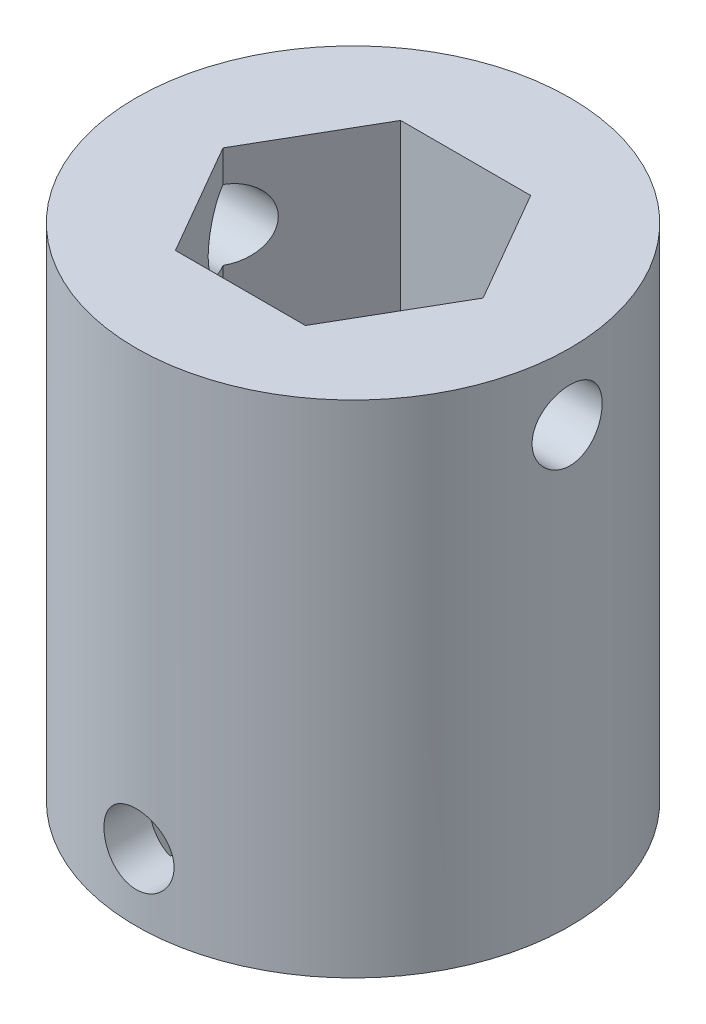
SolidWorks part; units mm, degrees
ref_plane "Front Plane" through (0, 0, 0) normal (0, 0, 1) x (1, 0, 0)
ref_plane "Top Plane" through (0, 0, 0) normal (0, 1, 0) x (1, 0, 0)
ref_plane "Right Plane" through (0, 0, 0) normal (1, 0, 0) x (0, 0, -1)
sketch "Sketch1" plane through (0, 0, 0) normal (0, 1, 0) x (1, 0, 0)
  line L1 (7.7942, 0) -> (3.8971, 6.75)
  line L2 (3.8971, 6.75) -> (-3.8971, 6.75)
  line L3 (-3.8971, 6.75) -> (-7.7942, 0)
  line L4 (-7.7942, 0) -> (-3.8971, -6.75)
  line L5 (-3.8971, -6.75) -> (3.8971, -6.75)
  line L6 (3.8971, -6.75) -> (7.7942, 0)
  circle A0 centre (0, 0) radius 13
  circle A1 centre (0, 0) radius 6.75 construction
  dimension "D2" = 26
  dimension "D1" = 13.5
extrude "Boss-Extrude1" add sketch "Sketch1" along normal blind 15
sketch "Sketch2" plane through (0, 0, 0) normal (0, -1, 0) x (1, 0, 0)
  circle A0 centre (0, 0) radius 13
  dimension "D1" = 26
extrude "Boss-Extrude2" add sketch "Sketch2" along normal blind 15
sketch "Sketch3" plane through (0, -15, 0) normal (0, -1, 0) x (1, 0, 0)
  arc A0 (-6.2438, 8.2671) -> (-5.2142, 5.3944) centre (2.4553, 9.7641) ccw
  arc A1 (-5.2142, 5.3944) -> (-5.5757, 5.0199) centre (0, 0) ccw
  arc A2 (-5.5757, 5.0199) -> (-8.483, 5.9471) centre (-9.671, -2.7995) ccw
  arc A3 (-8.483, 5.9471) -> (-9.2124, 4.7393) centre (0, 0) ccw
  arc A4 (-9.2124, 4.7393) -> (-7.0384, 2.5978) centre (-2.0244, 9.8624) ccw
  arc A5 (-7.0384, 2.5978) -> (-7.2016, 2.1036) centre (0, 0) ccw
  arc A6 (-7.2016, 2.1036) -> (-10.2233, 1.6775) centre (-7.4986, -6.7184) ccw
  arc A7 (-10.2233, 1.6775) -> (-10.3564, 0.2728) centre (0, 0) ccw
  arc A8 (-10.3564, 0.2728) -> (-7.4685, -0.7133) centre (-6.103, 8.0074) ccw
  arc A9 (-7.4685, -0.7133) -> (-7.4011, -1.2294) centre (0, 0) ccw
  arc A10 (-7.4011, -1.2294) -> (-9.9387, -2.9243) centre (-3.841, -9.3066) ccw
  arc A11 (-9.9387, -2.9243) -> (-9.4492, -4.2477) centre (0, 0) ccw
  arc A12 (-9.4492, -4.2477) -> (-6.4194, -3.8831) centre (-8.9729, 4.5664) ccw
  arc A13 (-6.4194, -3.8831) -> (-6.1347, -4.3188) centre (0, 0) ccw
  arc A14 (-6.1347, -4.3188) -> (-7.6857, -6.947) centre (0.5773, -10.0515) ccw
  arc A15 (-7.6857, -6.947) -> (-6.6704, -7.9269) centre (0, 0) ccw
  arc A16 (-6.6704, -7.9269) -> (-4.0989, -6.2838) centre (-10.0656, 0.221) ccw
  arc A17 (-4.0989, -6.2838) -> (-3.6533, -6.5529) centre (0, 0) ccw
  arc A18 (-3.6533, -6.5529) -> (-3.9104, -9.5937) centre (4.8813, -8.8056) ccw
  arc A19 (-3.9104, -9.5937) -> (-2.5705, -10.036) centre (0, 0) ccw
  arc A20 (-2.5705, -10.036) -> (-0.9665, -7.44) centre (-9.1647, -4.1682) ccw
  arc A21 (-0.9665, -7.44) -> (-0.4483, -7.4891) centre (0, 0) ccw
  arc A22 (-0.4483, -7.4891) -> (0.6394, -10.3402) centre (8.2185, -5.8156) ccw
  arc A23 (0.6394, -10.3402) -> (2.0385, -10.1575) centre (0, 0) ccw
  arc A24 (2.0385, -10.1575) -> (2.3573, -7.1225) centre (-6.4486, -7.7318) ccw
  arc A25 (2.3573, -7.1225) -> (2.8455, -6.942) centre (0, 0) ccw
  arc A26 (2.8455, -6.942) -> (5.0626, -9.0388) centre (9.9279, -1.6738) ccw
  arc A27 (5.0626, -9.0388) -> (6.2438, -8.2671) centre (0, 0) ccw
  arc A28 (6.2438, -8.2671) -> (5.2142, -5.3944) centre (-2.4553, -9.7641) ccw
  arc A29 (5.2142, -5.3944) -> (5.5757, -5.0199) centre (0, 0) ccw
  arc A30 (5.5757, -5.0199) -> (8.483, -5.9471) centre (9.671, 2.7995) ccw
  arc A31 (8.483, -5.9471) -> (9.2124, -4.7393) centre (0, 0) ccw
  arc A32 (9.2124, -4.7393) -> (7.0384, -2.5978) centre (2.0244, -9.8624) ccw
  arc A33 (7.0384, -2.5978) -> (7.2016, -2.1036) centre (0, 0) ccw
  arc A34 (7.2016, -2.1036) -> (10.2233, -1.6775) centre (7.4986, 6.7184) ccw
  arc A35 (10.2233, -1.6775) -> (10.3564, -0.2728) centre (0, 0) ccw
  arc A36 (10.3564, -0.2728) -> (7.4685, 0.7133) centre (6.103, -8.0074) ccw
  arc A37 (7.4685, 0.7133) -> (7.4011, 1.2294) centre (0, 0) ccw
  arc A38 (7.4011, 1.2294) -> (9.9387, 2.9243) centre (3.841, 9.3066) ccw
  arc A39 (9.9387, 2.9243) -> (9.4492, 4.2477) centre (0, 0) ccw
  arc A40 (9.4492, 4.2477) -> (6.4194, 3.8831) centre (8.9729, -4.5664) ccw
  arc A41 (6.4194, 3.8831) -> (6.1347, 4.3188) centre (0, 0) ccw
  arc A42 (6.1347, 4.3188) -> (7.6857, 6.947) centre (-0.5773, 10.0515) ccw
  arc A43 (7.6857, 6.947) -> (6.6704, 7.9269) centre (0, 0) ccw
  arc A44 (6.6704, 7.9269) -> (4.0989, 6.2838) centre (10.0656, -0.221) ccw
  arc A45 (4.0989, 6.2838) -> (3.6533, 6.5529) centre (0, 0) ccw
  arc A46 (3.6533, 6.5529) -> (3.9104, 9.5937) centre (-4.8813, 8.8056) ccw
  arc A47 (3.9104, 9.5937) -> (2.5705, 10.036) centre (0, 0) ccw
  arc A48 (2.5705, 10.036) -> (0.9665, 7.44) centre (9.1647, 4.1682) ccw
  arc A49 (0.9665, 7.44) -> (0.4483, 7.4891) centre (0, 0) ccw
  arc A50 (0.4483, 7.4891) -> (-0.6394, 10.3402) centre (-8.2185, 5.8156) ccw
  arc A51 (-0.6394, 10.3402) -> (-2.0385, 10.1575) centre (0, 0) ccw
  arc A52 (-2.0385, 10.1575) -> (-2.3573, 7.1225) centre (6.4486, 7.7318) ccw
  arc A53 (-2.3573, 7.1225) -> (-2.8455, 6.942) centre (0, 0) ccw
  arc A54 (-2.8455, 6.942) -> (-5.0626, 9.0388) centre (-9.9279, 1.6738) ccw
  arc A55 (-5.0626, 9.0388) -> (-6.2438, 8.2671) centre (0, 0) ccw
  arc A57 (-5.5304, 4.7688) -> (-8.3889, 5.7316) centre (-9.671, -2.7995) ccw
  arc A58 (-4.9617, 5.358) -> (-5.5304, 4.7688) centre (0, 0) ccw
  arc A59 (-6.0251, 8.1807) -> (-4.9617, 5.358) centre (2.4553, 9.7641) ccw
  arc A60 (-5.0713, 8.8038) -> (-6.0251, 8.1807) centre (0, 0) ccw
  arc A61 (-2.9136, 6.6961) -> (-5.0713, 8.8038) centre (-9.9279, 1.6738) ccw
  arc A62 (-2.1455, 6.9802) -> (-2.9136, 6.6961) centre (0, 0) ccw
  arc A63 (-1.879, 9.9847) -> (-2.1455, 6.9802) centre (6.4486, 7.7318) ccw
  arc A64 (-0.7492, 10.1323) -> (-1.879, 9.9847) centre (0, 0) ccw
  arc A65 (0.2803, 7.2971) -> (-0.7492, 10.1323) centre (-8.2185, 5.8156) ccw
  arc A66 (1.0955, 7.2199) -> (0.2803, 7.2971) centre (0, 0) ccw
  arc A67 (2.6393, 9.8112) -> (1.0955, 7.2199) centre (9.1647, 4.1682) ccw
  arc A68 (3.7212, 9.454) -> (2.6393, 9.8112) centre (0, 0) ccw
  arc A69 (3.4186, 6.4529) -> (3.7212, 9.454) centre (-4.8813, 8.8056) ccw
  arc A70 (4.1196, 6.0295) -> (3.4186, 6.4529) centre (0, 0) ccw
  arc A71 (6.6349, 7.6944) -> (4.1196, 6.0295) centre (10.0656, -0.221) ccw
  arc A72 (7.4546, 6.9032) -> (6.6349, 7.6944) centre (0, 0) ccw
  arc A73 (5.8799, 4.3306) -> (7.4546, 6.9032) centre (-0.5773, 10.0515) ccw
  arc A74 (6.3278, 3.645) -> (5.8799, 4.3306) centre (0, 0) ccw
  arc A75 (9.3163, 4.0537) -> (6.3278, 3.645) centre (8.9729, -4.5664) ccw
  arc A76 (9.7116, 2.9851) -> (9.3163, 4.0537) centre (0, 0) ccw
  arc A77 (7.1765, 1.3505) -> (9.7116, 2.9851) centre (3.841, 9.3066) ccw
  arc A78 (7.2826, 0.5385) -> (7.1765, 1.3505) centre (0, 0) ccw
  arc A79 (10.1525, -0.3899) -> (7.2826, 0.5385) centre (6.103, -8.0074) ccw
  arc A80 (10.045, -1.5242) -> (10.1525, -0.3899) centre (0, 0) ccw
  arc A81 (7.0518, -1.897) -> (10.045, -1.5242) centre (7.4986, 6.7184) ccw
  arc A82 (6.7951, -2.6746) -> (7.0518, -1.897) centre (0, 0) ccw
  arc A83 (8.9779, -4.7563) -> (6.7951, -2.6746) centre (2.0244, -9.8624) ccw
  arc A84 (8.3889, -5.7316) -> (8.9779, -4.7563) centre (0, 0) ccw
  arc A85 (5.5304, -4.7688) -> (8.3889, -5.7316) centre (9.671, 2.7995) ccw
  arc A86 (4.9617, -5.358) -> (5.5304, -4.7688) centre (0, 0) ccw
  arc A87 (6.0251, -8.1807) -> (4.9617, -5.358) centre (-2.4553, -9.7641) ccw
  arc A88 (5.0713, -8.8038) -> (6.0251, -8.1807) centre (0, 0) ccw
  arc A89 (2.9136, -6.6961) -> (5.0713, -8.8038) centre (9.9279, -1.6738) ccw
  arc A90 (2.1455, -6.9802) -> (2.9136, -6.6961) centre (0, 0) ccw
  arc A91 (1.879, -9.9847) -> (2.1455, -6.9802) centre (-6.4486, -7.7318) ccw
  arc A92 (0.7492, -10.1323) -> (1.879, -9.9847) centre (0, 0) ccw
  arc A93 (-0.2803, -7.2971) -> (0.7492, -10.1323) centre (8.2185, -5.8156) ccw
  arc A94 (-1.0955, -7.2199) -> (-0.2803, -7.2971) centre (0, 0) ccw
  arc A95 (-2.6393, -9.8112) -> (-1.0955, -7.2199) centre (-9.1647, -4.1682) ccw
  arc A96 (-3.7212, -9.454) -> (-2.6393, -9.8112) centre (0, 0) ccw
  arc A97 (-3.4186, -6.4529) -> (-3.7212, -9.454) centre (4.8813, -8.8056) ccw
  arc A98 (-4.1196, -6.0295) -> (-3.4186, -6.4529) centre (0, 0) ccw
  arc A99 (-6.6349, -7.6944) -> (-4.1196, -6.0295) centre (-10.0656, 0.221) ccw
  arc A100 (-7.4546, -6.9032) -> (-6.6349, -7.6944) centre (0, 0) ccw
  arc A101 (-5.8799, -4.3306) -> (-7.4546, -6.9032) centre (0.5773, -10.0515) ccw
  arc A102 (-6.3278, -3.645) -> (-5.8799, -4.3306) centre (0, 0) ccw
  arc A103 (-9.3163, -4.0537) -> (-6.3278, -3.645) centre (-8.9729, 4.5664) ccw
  arc A104 (-9.7116, -2.9851) -> (-9.3163, -4.0537) centre (0, 0) ccw
  arc A105 (-7.1765, -1.3505) -> (-9.7116, -2.9851) centre (-3.841, -9.3066) ccw
  arc A106 (-7.2826, -0.5385) -> (-7.1765, -1.3505) centre (0, 0) ccw
  arc A107 (-10.1525, 0.3899) -> (-7.2826, -0.5385) centre (-6.103, 8.0074) ccw
  arc A108 (-10.045, 1.5242) -> (-10.1525, 0.3899) centre (0, 0) ccw
  arc A109 (-7.0518, 1.897) -> (-10.045, 1.5242) centre (-7.4986, -6.7184) ccw
  arc A110 (-6.7951, 2.6746) -> (-7.0518, 1.897) centre (0, 0) ccw
  arc A111 (-8.9779, 4.7563) -> (-6.7951, 2.6746) centre (-2.0244, 9.8624) ccw
  arc A112 (-8.3889, 5.7316) -> (-8.9779, 4.7563) centre (0, 0) ccw
  arc A113 (-5.5304, 4.7688) -> (-8.3889, 5.7316) centre (-9.671, -2.7995) ccw construction
  arc A114 (-4.9617, 5.358) -> (-5.5304, 4.7688) centre (0, 0) ccw construction
  arc A115 (-6.0251, 8.1807) -> (-4.9617, 5.358) centre (2.4553, 9.7641) ccw construction
  arc A116 (-5.0713, 8.8038) -> (-6.0251, 8.1807) centre (0, 0) ccw construction
  arc A117 (-2.9136, 6.6961) -> (-5.0713, 8.8038) centre (-9.9279, 1.6738) ccw construction
  arc A118 (-2.1455, 6.9802) -> (-2.9136, 6.6961) centre (0, 0) ccw construction
  arc A119 (-1.879, 9.9847) -> (-2.1455, 6.9802) centre (6.4486, 7.7318) ccw construction
  arc A120 (-0.7492, 10.1323) -> (-1.879, 9.9847) centre (0, 0) ccw construction
  arc A121 (0.2803, 7.2971) -> (-0.7492, 10.1323) centre (-8.2185, 5.8156) ccw construction
  arc A122 (1.0955, 7.2199) -> (0.2803, 7.2971) centre (0, 0) ccw construction
  arc A123 (2.6393, 9.8112) -> (1.0955, 7.2199) centre (9.1647, 4.1682) ccw construction
  arc A124 (3.7212, 9.454) -> (2.6393, 9.8112) centre (0, 0) ccw construction
  arc A125 (3.4186, 6.4529) -> (3.7212, 9.454) centre (-4.8813, 8.8056) ccw construction
  arc A126 (4.1196, 6.0295) -> (3.4186, 6.4529) centre (0, 0) ccw construction
  arc A127 (6.6349, 7.6944) -> (4.1196, 6.0295) centre (10.0656, -0.221) ccw construction
  arc A128 (7.4546, 6.9032) -> (6.6349, 7.6944) centre (0, 0) ccw construction
  arc A129 (5.8799, 4.3306) -> (7.4546, 6.9032) centre (-0.5773, 10.0515) ccw construction
  arc A130 (6.3278, 3.645) -> (5.8799, 4.3306) centre (0, 0) ccw construction
  arc A131 (9.3163, 4.0537) -> (6.3278, 3.645) centre (8.9729, -4.5664) ccw construction
  arc A132 (9.7116, 2.9851) -> (9.3163, 4.0537) centre (0, 0) ccw construction
  arc A133 (7.1765, 1.3505) -> (9.7116, 2.9851) centre (3.841, 9.3066) ccw construction
  arc A134 (7.2826, 0.5385) -> (7.1765, 1.3505) centre (0, 0) ccw construction
  arc A135 (10.1525, -0.3899) -> (7.2826, 0.5385) centre (6.103, -8.0074) ccw construction
  arc A136 (10.045, -1.5242) -> (10.1525, -0.3899) centre (0, 0) ccw construction
  arc A137 (7.0518, -1.897) -> (10.045, -1.5242) centre (7.4986, 6.7184) ccw construction
  arc A138 (6.7951, -2.6746) -> (7.0518, -1.897) centre (0, 0) ccw construction
  arc A139 (8.9779, -4.7563) -> (6.7951, -2.6746) centre (2.0244, -9.8624) ccw construction
  arc A140 (8.3889, -5.7316) -> (8.9779, -4.7563) centre (0, 0) ccw construction
  arc A141 (5.5304, -4.7688) -> (8.3889, -5.7316) centre (9.671, 2.7995) ccw construction
  arc A142 (4.9617, -5.358) -> (5.5304, -4.7688) centre (0, 0) ccw construction
  arc A143 (6.0251, -8.1807) -> (4.9617, -5.358) centre (-2.4553, -9.7641) ccw construction
  arc A144 (5.0713, -8.8038) -> (6.0251, -8.1807) centre (0, 0) ccw construction
  arc A145 (2.9136, -6.6961) -> (5.0713, -8.8038) centre (9.9279, -1.6738) ccw construction
  arc A146 (2.1455, -6.9802) -> (2.9136, -6.6961) centre (0, 0) ccw construction
  arc A147 (1.879, -9.9847) -> (2.1455, -6.9802) centre (-6.4486, -7.7318) ccw construction
  arc A148 (0.7492, -10.1323) -> (1.879, -9.9847) centre (0, 0) ccw construction
  arc A149 (-0.2803, -7.2971) -> (0.7492, -10.1323) centre (8.2185, -5.8156) ccw construction
  arc A150 (-1.0955, -7.2199) -> (-0.2803, -7.2971) centre (0, 0) ccw construction
  arc A151 (-2.6393, -9.8112) -> (-1.0955, -7.2199) centre (-9.1647, -4.1682) ccw construction
  arc A152 (-3.7212, -9.454) -> (-2.6393, -9.8112) centre (0, 0) ccw construction
  arc A153 (-3.4186, -6.4529) -> (-3.7212, -9.454) centre (4.8813, -8.8056) ccw construction
  arc A154 (-4.1196, -6.0295) -> (-3.4186, -6.4529) centre (0, 0) ccw construction
  arc A155 (-6.6349, -7.6944) -> (-4.1196, -6.0295) centre (-10.0656, 0.221) ccw construction
  arc A156 (-7.4546, -6.9032) -> (-6.6349, -7.6944) centre (0, 0) ccw construction
  arc A157 (-5.8799, -4.3306) -> (-7.4546, -6.9032) centre (0.5773, -10.0515) ccw construction
  arc A158 (-6.3278, -3.645) -> (-5.8799, -4.3306) centre (0, 0) ccw construction
  arc A159 (-9.3163, -4.0537) -> (-6.3278, -3.645) centre (-8.9729, 4.5664) ccw construction
  arc A160 (-9.7116, -2.9851) -> (-9.3163, -4.0537) centre (0, 0) ccw construction
  arc A161 (-7.1765, -1.3505) -> (-9.7116, -2.9851) centre (-3.841, -9.3066) ccw construction
  arc A162 (-7.2826, -0.5385) -> (-7.1765, -1.3505) centre (0, 0) ccw construction
  arc A163 (-10.1525, 0.3899) -> (-7.2826, -0.5385) centre (-6.103, 8.0074) ccw construction
  arc A164 (-10.045, 1.5242) -> (-10.1525, 0.3899) centre (0, 0) ccw construction
  arc A165 (-7.0518, 1.897) -> (-10.045, 1.5242) centre (-7.4986, -6.7184) ccw construction
  arc A166 (-6.7951, 2.6746) -> (-7.0518, 1.897) centre (0, 0) ccw construction
  arc A167 (-8.9779, 4.7563) -> (-6.7951, 2.6746) centre (-2.0244, 9.8624) ccw construction
  arc A168 (-8.3889, 5.7316) -> (-8.9779, 4.7563) centre (0, 0) ccw construction
  dimension "D1" = 0
  dimension "D2" = 0.2
extrude "Cut-Extrude1" cut sketch "Sketch3" against normal blind 15
sketch "Sketch4" plane through (0, 0, 0) normal (0, 0, 1) x (1, 0, 0)
  line L0 (-13, -15) -> (13, -15) construction
  circle A0 centre (0, -11) radius 2.1
  dimension "D1" = 4.2
  dimension "D2" = 4
extrude "Cut-Extrude2" cut sketch "Sketch4" against normal through all and the other way through all
sketch "Sketch5" plane through (0, 0, 0) normal (1, 0, 0) x (0, 0, -1)
  line L0 (13, 15) -> (-13, 15) construction
  circle A0 centre (0, 11) radius 2.1
  dimension "D2" = 4.2
  dimension "D1" = 4
extrude "Cut-Extrude3" cut sketch "Sketch5" against normal through all and the other way through all
